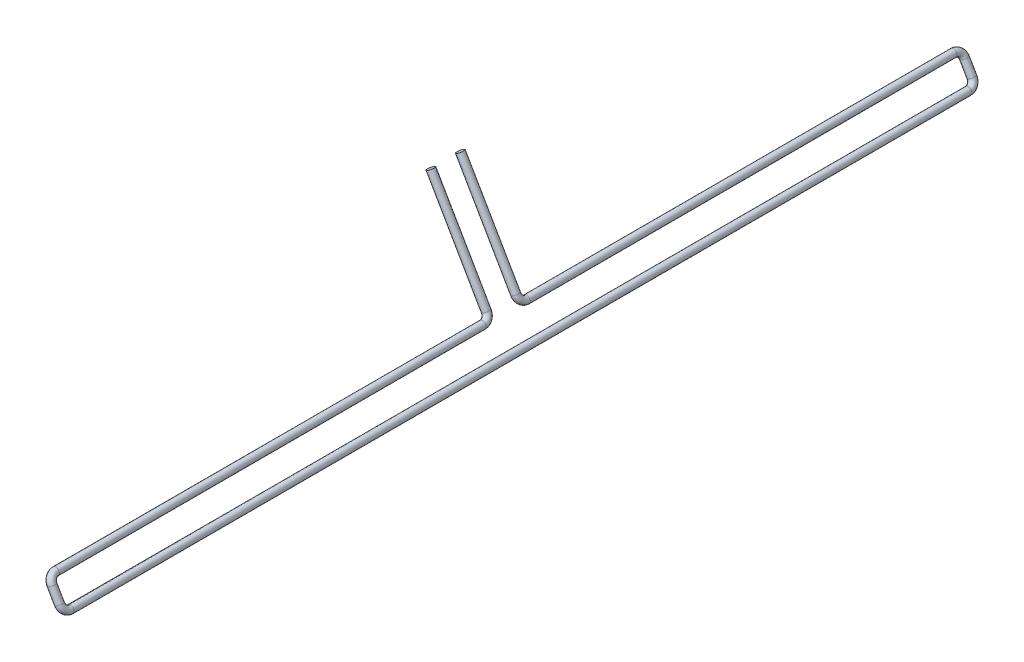
SolidWorks part; units mm, degrees
ref_plane "Front Plane" through (0, 0, 0) normal (0, 0, 1) x (1, 0, 0)
ref_plane "Top Plane" through (0, 0, 0) normal (0, 1, 0) x (1, 0, 0)
ref_plane "Right Plane" through (0, 0, 0) normal (1, 0, 0) x (0, 0, -1)
sketch "Sketch1" plane through (0, 0, 0) normal (0, 0, 1) x (1, 0, 0)
  circle A0 centre (31.5371, 3.1679) radius 0.75
sketch "Sketch2" plane through (25.0245, 14.4479, -100.9821) normal (-0.866, -0.5, 0) x (0.5, -0.866, 0)
  line L0 (13.0251, 100.9821) -> (13.0251, 192.5021) construction
  line L1 (11.5251, 194.0021) -> (8.5176, 194.0021) construction
  line L2 (7.0176, 192.5021) -> (7.0176, 105.4821) construction
  line L3 (5.5176, 103.9821) -> (-17.0505, 103.9821) construction
  line L4 (13.0251, 100.9821) -> (13.0251, 192.5021)
  line L5 (11.5251, 194.0021) -> (8.5176, 194.0021)
  line L6 (7.0176, 192.5021) -> (7.0176, 105.4821)
  line L7 (5.5176, 103.9821) -> (-17.0505, 103.9821)
  arc A0 (13.0251, 192.5021) -> (11.5251, 194.0021) centre (11.5251, 192.5021) ccw construction
  arc A1 (8.5176, 194.0021) -> (7.0176, 192.5021) centre (8.5176, 192.5021) ccw construction
  arc A2 (5.5176, 103.9821) -> (7.0176, 105.4821) centre (5.5176, 105.4821) ccw construction
  arc A3 (13.0251, 192.5021) -> (11.5251, 194.0021) centre (11.5251, 192.5021) ccw
  arc A4 (8.5176, 194.0021) -> (7.0176, 192.5021) centre (8.5176, 192.5021) ccw
  arc A5 (5.5176, 103.9821) -> (7.0176, 105.4821) centre (5.5176, 105.4821) ccw
sweep "Sweep1" add profiles "Sketch1" path "Sketch2"
mirror "Mirror1" about plane through (0, 0, 0) normal (0, 0, 1) of "Sweep1"
